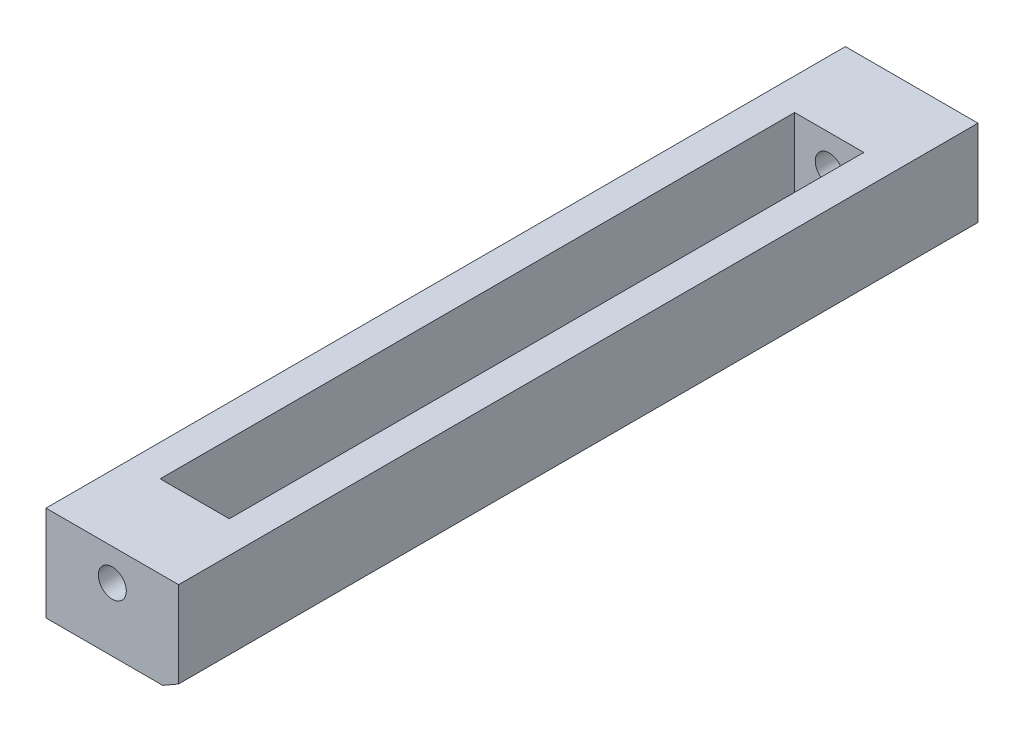
SolidWorks part; units mm, degrees
ref_plane "Front Plane" through (0, 0, 0) normal (0, 0, 1) x (1, 0, 0)
ref_plane "Top Plane" through (0, 0, 0) normal (0, 1, 0) x (1, 0, 0)
ref_plane "Right Plane" through (0, 0, 0) normal (1, 0, 0) x (0, 0, -1)
sketch "Sketch1" plane through (0, 0, 0) normal (0, 1, 0) x (1, 0, 0)
  line L1 (-6.6357, -40) -> (6.6358, -40)
  line L2 (-6.6357, -40) -> (-6.6357, 40)
  line L3 (-6.6357, 40) -> (6.6358, 40)
  line L4 (6.6358, -40) -> (6.6358, 40)
  line L5 (-6.6357, -40) -> (6.6358, 40) construction
  line L6 (-6.6357, 40) -> (6.6358, -40) construction
  line L11 (-3.4607, -31.75) -> (3.4608, -31.75)
  line L12 (-3.4607, -31.75) -> (-3.4607, 31.75)
  line L13 (-3.4607, 31.75) -> (3.4608, 31.75)
  line L14 (3.4608, -31.75) -> (3.4608, 31.75)
  line L15 (-3.4607, -31.75) -> (3.4608, 31.75) construction
  line L16 (-3.4607, 31.75) -> (3.4608, -31.75) construction
  point P0 (0, 0)
  point P6 (0, 0)
  dimension "D1" = 13.2715
  dimension "D2" = 80
  dimension "D3" = 3.175
  dimension "D4" = 63.5
extrude "Boss-Extrude1" add sketch "Sketch1" along normal blind 3.175 and the other way blind 6.35
sketch "Sketch4" plane through (0, 0, 40) normal (0, 0, 1) x (1, 0, 0)
  circle A0 centre (0, 0) radius 1.4
  dimension "D1" = 2.8
extrude "Cut-Extrude1" cut sketch "Sketch4" against normal through all
chamfer "Chamfer1" distance 1.5875 angle 30 1 edges at (6.6358, -6.35, 0)
equation "\"tighttol\" = 0.005in"
equation "\"normtol\" = 0.01in"
equation "\"loosetol\" = 0.02in"
equation "\"Fry height\"= 0.5in"
equation "\"Fry spacing\"= 0.5625in"
equation "\"Potato width\"= \"Fry spacing\" * 4"
equation "\"Potato length\"= 80mm"
equation "\"D1@Sketch1\"=\"Fry spacing\" - 2 * \"loosetol\""
equation "\"D2@Sketch1\"=\"Potato length\""
equation "\"D1@Sketch4\"=2.8mm"
